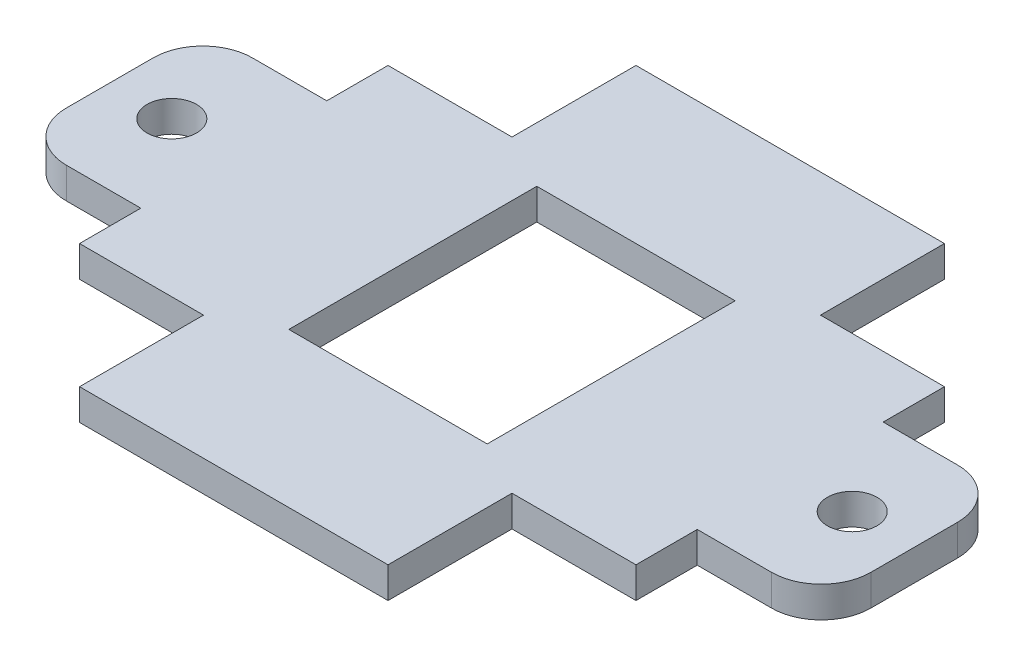
SolidWorks part; units mm, degrees
ref_plane "Front Plane" through (0, 0, 0) normal (0, 0, 1) x (1, 0, 0)
ref_plane "Top Plane" through (0, 0, 0) normal (0, 1, 0) x (1, 0, 0)
ref_plane "Right Plane" through (0, 0, 0) normal (1, 0, 0) x (0, 0, -1)
sketch "Sketch1" plane through (0, 0, 0) normal (0, 1, 0) x (1, 0, 0)
  line L5 (15.8, 15.8) -> (-15.8, -15.8) construction
  line L6 (-28.5, 15.8) -> (-28.5, 9.525)
  line L15 (-28.5, -9.525) -> (-36.12, -9.525)
  line L17 (-28.5, 9.525) -> (-36.12, 9.525)
  line L18 (-41.2, -4.445) -> (-41.2, 4.445)
  line L19 (-15.8, 28.5) -> (15.8, 28.5)
  line L20 (15.8, -28.5) -> (-15.8, -28.5)
  line L22 (15.8, -15.8) -> (-15.8, 15.8) construction
  line L23 (0, -28.5) -> (0, 28.5) construction
  line L24 (28.5, -9.525) -> (36.12, -9.525)
  line L25 (41.2, -4.445) -> (41.2, 4.445)
  line L26 (28.5, 9.525) -> (36.12, 9.525)
  line L29 (-15.8, 15.8) -> (-28.5, 15.8)
  line L30 (-15.8, 15.8) -> (-15.8, 28.5)
  line L35 (15.8, 15.8) -> (28.5, 15.8)
  line L36 (15.8, 15.8) -> (15.8, 28.5)
  line L39 (-28.5, -9.525) -> (-28.5, -15.8)
  line L40 (28.5, 15.8) -> (28.5, 9.525)
  line L41 (15.8, -15.8) -> (28.5, -15.8)
  line L42 (15.8, -15.8) -> (15.8, -28.5)
  line L45 (28.5, -9.525) -> (28.5, -15.8)
  line L47 (-15.8, -15.8) -> (-28.5, -15.8)
  line L48 (-15.8, -15.8) -> (-15.8, -28.5)
  line L49 (10.16, -12.7) -> (-10.16, -12.7)
  line L50 (10.16, -12.7) -> (10.16, 12.7)
  line L51 (10.16, 12.7) -> (-10.16, 12.7)
  line L52 (-10.16, -12.7) -> (-10.16, 12.7)
  line L53 (10.16, -12.7) -> (-10.16, 12.7) construction
  line L54 (10.16, 12.7) -> (-10.16, -12.7) construction
  circle A13 centre (-34.85, 0) radius 2.54
  arc A14 (36.12, -9.525) -> (41.2, -4.445) centre (36.12, -4.445) ccw
  arc A15 (41.2, 4.445) -> (36.12, 9.525) centre (36.12, 4.445) ccw
  arc A16 (-36.12, 9.525) -> (-41.2, 4.445) centre (-36.12, 4.445) ccw
  arc A17 (-36.12, -9.525) -> (-41.2, -4.445) centre (-36.12, -4.445) cw
  circle A18 centre (34.85, 0) radius 2.54
  point P0 (0, 0)
  point P9 (-28.5, 0)
  point P38 (0, 0)
  point P55 (41.2, -9.525)
  point P58 (41.2, 9.525)
  dimension "D4" = 12.7
  dimension "D5" = 20.32
  dimension "D6" = 12.7
  dimension "D10" = 6.35
  dimension "D12" = 5.08
  dimension "D13" = 5.08
  dimension "D2" = 12.7
  dimension "D3" = 82.4
  dimension "D7" = 12.7
  dimension "D9" = 19.05
  dimension "D11" = 9.525
  dimension "D8" = 12.7
  dimension "D14" = 12.7
  dimension "D15" = 25.4
extrude "Boss-Extrude1" add sketch "Sketch1" along normal blind 3.175
